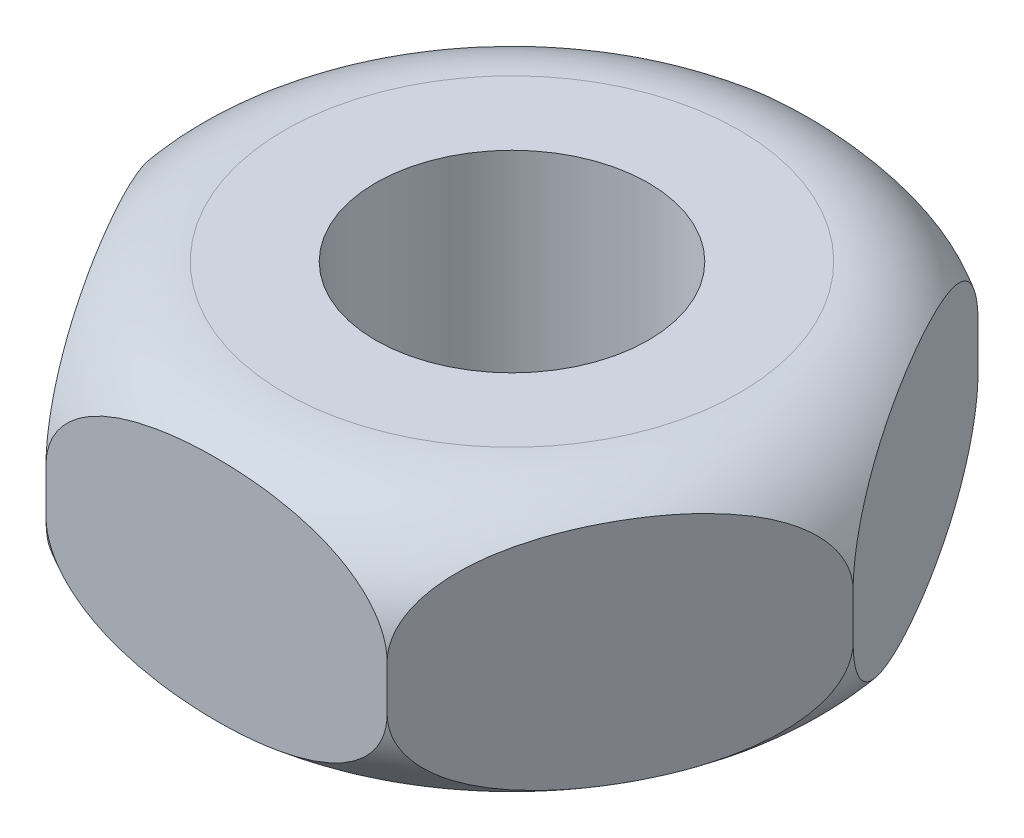
SolidWorks part; units mm, degrees
ref_plane "Front Plane" through (0, 0, 0) normal (0, 0, 1) x (1, 0, 0)
ref_plane "Top Plane" through (0, 0, 0) normal (0, 1, 0) x (1, 0, 0)
ref_plane "Right Plane" through (0, 0, 0) normal (1, 0, 0) x (0, 0, -1)
sketch "Sketch1" plane through (0, 0, 0) normal (0, 1, 0) x (1, 0, 0)
  line L1 (15.0111, 0) -> (7.5056, 13)
  line L2 (7.5056, 13) -> (-7.5056, 13)
  line L3 (-7.5056, 13) -> (-15.0111, 0)
  line L4 (-15.0111, 0) -> (-7.5056, -13)
  line L5 (-7.5056, -13) -> (7.5056, -13)
  line L6 (7.5056, -13) -> (15.0111, 0)
  circle A0 centre (0, 0) radius 13 construction
  circle A1 centre (0, 0) radius 6
  dimension "D2" = 12
  dimension "D1" = 26
extrude "Boss-Extrude1" add sketch "Sketch1" along normal mid plane 12
sketch "Sketch2" plane through (0, 0, 0) normal (0, 0, 1) x (1, 0, 0)
  line L0 (15.0111, 6) -> (15.0111, -6) construction
  line L1 (7.5056, 6) -> (15.0111, 6) construction
  line L2 (15.0111, 1) -> (15.0111, 6)
  line L3 (15.0111, 6) -> (10.0111, 6)
  line L4 (0, -5.4496) -> (0, 22.7117) construction
  arc A0 (15.0111, 1) -> (10.0111, 6) centre (10.0111, 1) ccw
  dimension "D1" = 5
revolve "Cut-Revolve1" cut sketch "Sketch2" angle 360 about L4
mirror "Mirror1" about plane through (0, 0, 0) normal (0, 1, 0) of "Cut-Revolve1"
